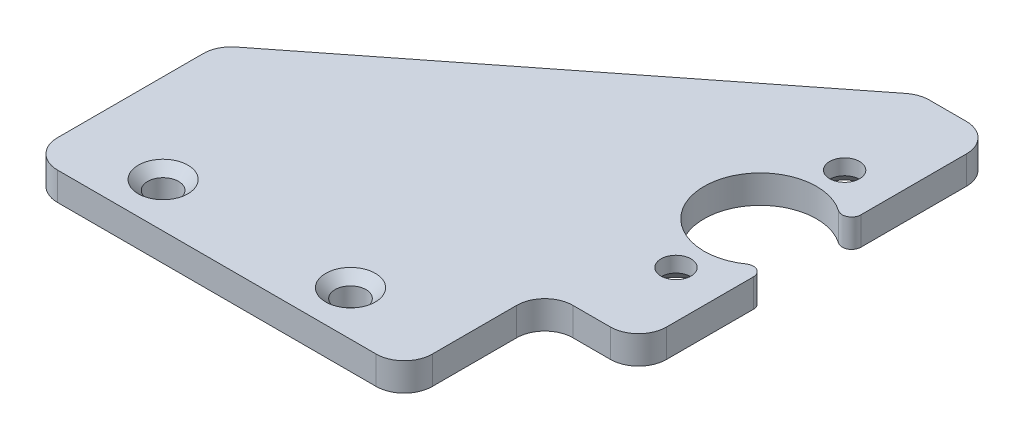
SolidWorks part; units mm, degrees
ref_plane "Plano frontal" through (0, 0, 0) normal (0, 0, 1) x (1, 0, 0)
ref_plane "Plano superior" through (0, 0, 0) normal (0, 1, 0) x (1, 0, 0)
ref_plane "Plano direito" through (0, 0, 0) normal (1, 0, 0) x (0, 0, -1)
sketch "Esboço1" plane through (0, 0, 0) normal (0, 1, 0) x (1, 0, 0)
  line L0 (0, 0) -> (25, 0) construction
  line L1 (0, 0) -> (0, 20) construction
  line L2 (-25, 20) -> (25, 20)
  line L5 (25, -20) -> (-25, -20)
  line L6 (-25, -20) -> (-25, 20)
  line L7 (25, 20) -> (25, -20)
  line L8 (25, 0.0001) -> (24.9995, 0.0001)
  line L9 (24.9995, -0.0001) -> (25, -0.0001)
  line L10 (24.9995, 0.0001) -> (24.9995, -0.0001)
  line L11 (25, -0.0001) -> (25, 0.0001)
  circle A0 centre (20, 9) radius 1.6
  circle A1 centre (20, -9) radius 1.6
  circle A2 centre (20, 0) radius 6
  point P3 (-25, 0)
  point P7 (0, 20)
  dimension "D4" = 3.2
  dimension "D6" = 12
  dimension "D1" = 50
  dimension "D2" = 40
  dimension "D3" = 0
  dimension "D5" = 18
  dimension "D7" = 5
  dimension "D8" = 5
extrude "Ressalto-extrusão10" add sketch "Esboço1" along normal blind 3 contours A2 L7 L2 L6 L5 A1 A0
fillet "Filete2" radius 1 2 edges at (25, 1.5, -3.3166) (25, 1.5, 3.3166)
chamfer "Chanfro1" distance 1.35 angle 45 2 edges at (20, 0, -7.4) (20, 0, 10.6)
sketch "Esboço5" plane through (0, 0, 0) normal (0, -1, 0) x (1, 0, 0)
  line L0 (-25, 20) -> (-25, 33)
  line L1 (-25, 33) -> (25, 33)
  line L2 (25, 33) -> (25, 20)
  line L3 (25, 20) -> (-25, 20)
  dimension "D1" = 13
extrude "Ressalto-extrusão13" add sketch "Esboço5" against normal blind 3
sketch "Esboço7" plane through (0, 0, 0) normal (0, -1, 0) x (1, 0, 0)
  line L0 (25, 5.7446) -> (25, 6.7446)
  line L1 (25, 5.7446) -> (25, 33) construction
  line L2 (25, 6.7446) -> (-25, 6.7446) construction
  line L3 (-25, 33) -> (-25, -20) construction
  line L4 (14, 0) -> (10, 0)
  line L5 (-15.5, 28.2346) -> (4.5, 28.2346) construction
  circle A0 centre (-15.5, 28.2346) radius 1.65
  circle A1 centre (4.5, 28.2346) radius 1.65
  arc A2 (23.4286, 4.9239) -> (23.4286, -4.9239) centre (20, 0) ccw construction
  dimension "D2" = 3.3
  dimension "D1" = 1
  dimension "D3" = 20
  dimension "D4" = 4
  dimension "D5" = 21.49
  dimension "D6" = 21.49
  dimension "D7" = 5.5
extrude "Corte-extrusão1" cut sketch "Esboço7" against normal through all contours A0 | A1
sketch "Esboço8" plane through (0, 0, 0) normal (0, -1, 0) x (1, 0, 0)
  line L0 (-25, -20) -> (-25, 13)
  line L1 (-25, 33) -> (-25, -20) construction
  line L2 (-25, 13) -> (17, -20)
  line L3 (-25, -20) -> (25, -20) construction
  line L4 (17, -20) -> (-25, -20)
  line L5 (25, 33) -> (25, 18)
  line L6 (25, 5.7446) -> (25, 33) construction
  line L7 (25, 18) -> (15, 18)
  line L8 (15, 18) -> (15, 33)
  line L9 (25, 33) -> (-25, 33) construction
  line L10 (15, 33) -> (25, 33)
  dimension "D1" = 20
  dimension "D2" = 8
  dimension "D3" = 15
  dimension "D4" = 10
extrude "Corte-extrusão2" cut sketch "Esboço8" against normal through all contours L4 L0 L2 | L10 L5 L7 L8
fillet "Filete3" radius 3 7 edges at (15, 1.5, 18) (-25, 1.5, 13) (-25, 1.5, 33) (15, 1.5, 33) (25, 1.5, 18) (25, 1.5, -20) (17, 1.5, -20)
chamfer "Chanfro2" distance 1 angle 45 2 edges at (4.5, 3, 26.5846) (-15.5, 3, 26.5846)
sketch "Esboço9" plane through (0, 0, 0) normal (0, -1, 0) x (1, 0, 0)
  line L0 (-15.5, 28.2346) -> (4.5, 28.2346) construction
  line L1 (-5.5, 28.2346) -> (-5.5, 10.2346) construction
  circle A0 centre (-5.5, 10.2346) radius 4
  dimension "D1" = 8
  dimension "D2" = 18
extrude "Ressalto-extrusão14" add sketch "Esboço9" along normal blind 8
